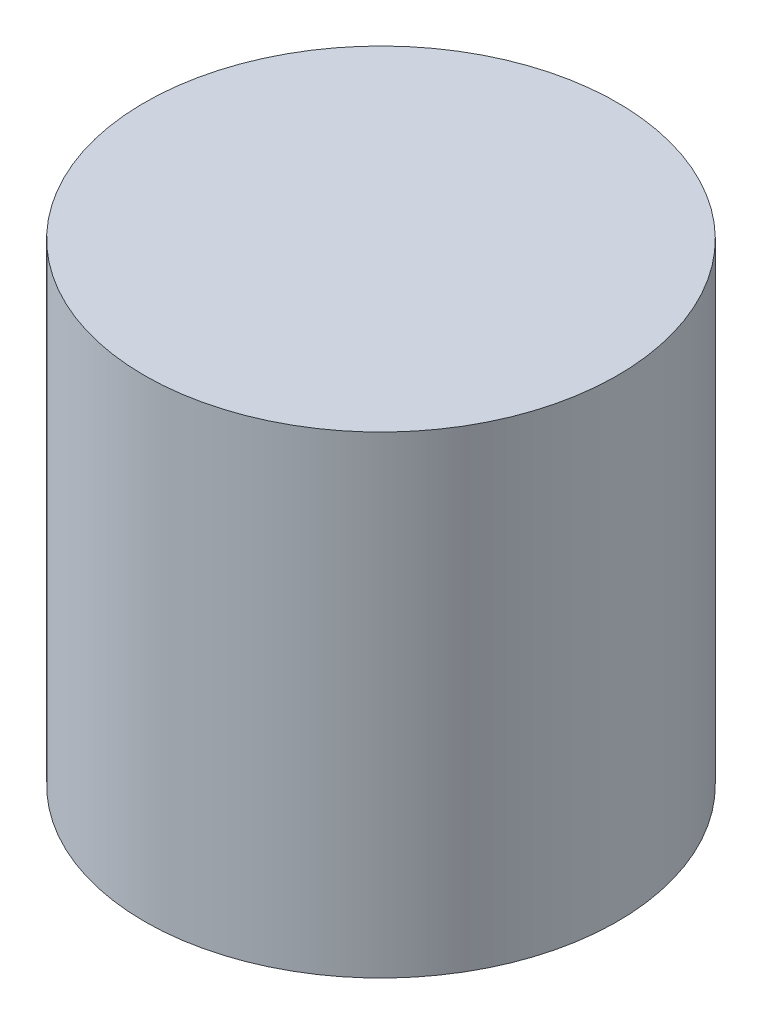
SolidWorks part; units mm, degrees
ref_plane "Front Plane" through (0, 0, 0) normal (0, 0, 1) x (1, 0, 0)
ref_plane "Top Plane" through (0, 0, 0) normal (0, 1, 0) x (1, 0, 0)
ref_plane "Right Plane" through (0, 0, 0) normal (1, 0, 0) x (0, 0, -1)
sketch "Sketch1" plane through (0, 0, 0) normal (0, 1, 0) x (1, 0, 0)
  circle A0 centre (0, 0) radius 76.2
  dimension "D1" = 152.4
extrude "Boss-Extrude1" add sketch "Sketch1" along normal blind 152.4
